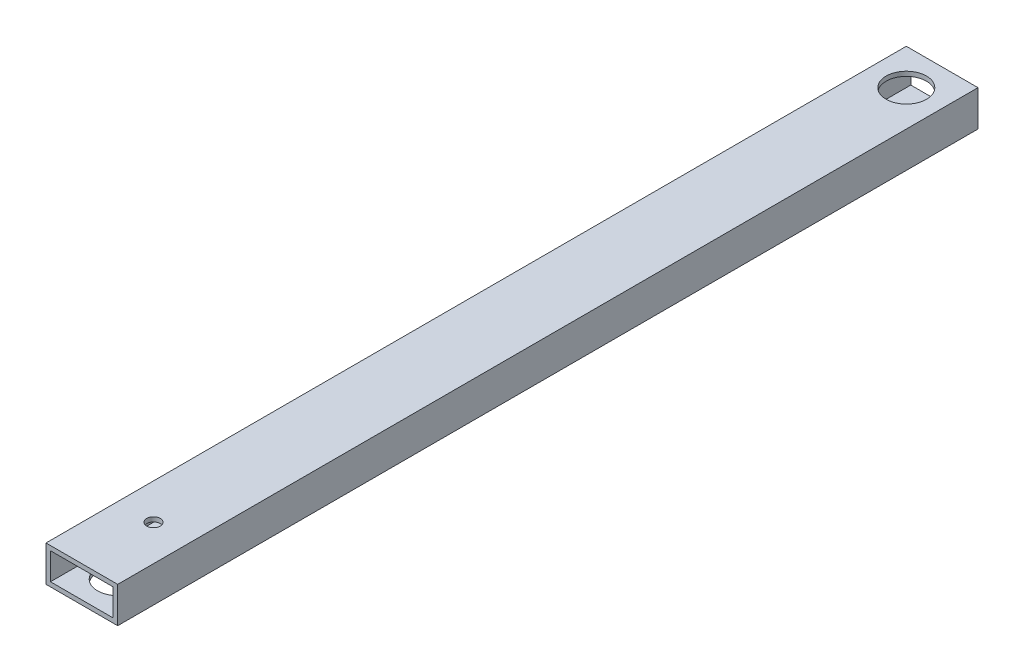
SolidWorks part; units mm, degrees
ref_plane "Front Plane" through (0, 0, 0) normal (0, 0, 1) x (1, 0, 0)
ref_plane "Top Plane" through (0, 0, 0) normal (0, 1, 0) x (1, 0, 0)
ref_plane "Right Plane" through (0, 0, 0) normal (1, 0, 0) x (0, 0, -1)
sketch "Sketch1" plane through (0, 0, 0) normal (0, 0, 1) x (1, 0, 0)
  line L1 (0, 0) -> (50.8, 0)
  line L2 (0, 0) -> (0, 25.4)
  line L3 (0, 25.4) -> (50.8, 25.4)
  line L4 (50.8, 0) -> (50.8, 25.4)
extrude "Boss-Extrude1" add sketch "Sketch1" along normal blind 609.6
sketch "Sketch2" plane through (0, 0, 0) normal (0, 0, -1) x (-1, 0, 0)
  line L1 (-3.175, 3.175) -> (-47.625, 3.175)
  line L2 (-3.175, 3.175) -> (-3.175, 22.225)
  line L3 (-3.175, 22.225) -> (-47.625, 22.225)
  line L4 (-47.625, 3.175) -> (-47.625, 22.225)
extrude "Cut-Extrude1" cut sketch "Sketch2" against normal blind 635
sketch "Sketch6" plane through (0, 25.4, 0) normal (0, 1, 0) x (1, 0, 0)
  line L0 (25.4, 0) -> (25.4, -25.4) construction
  line L1 (50.8, 0) -> (0, 0) construction
  circle A0 centre (25.4, -25.4) radius 14.2875
extrude "Cut-Extrude5" cut sketch "Sketch6" against normal blind 25.4
sketch "Sketch7" plane through (0, 0, 0) normal (0, -1, 0) x (1, 0, 0)
  circle A0 centre (25.4, 584.2) radius 14.2875
extrude "Cut-Extrude6" cut sketch "Sketch7" against normal blind 3.175
sketch "Sketch8" plane through (0, 25.4, 0) normal (0, 1, 0) x (1, 0, 0)
  line L0 (25.4, -609.6) -> (25.4, -558.8) construction
  line L1 (50.8, -609.6) -> (0, -609.6) construction
  circle A0 centre (25.4, -558.8) radius 4.7625
extrude "Cut-Extrude7" cut sketch "Sketch8" against normal blind 25.4
